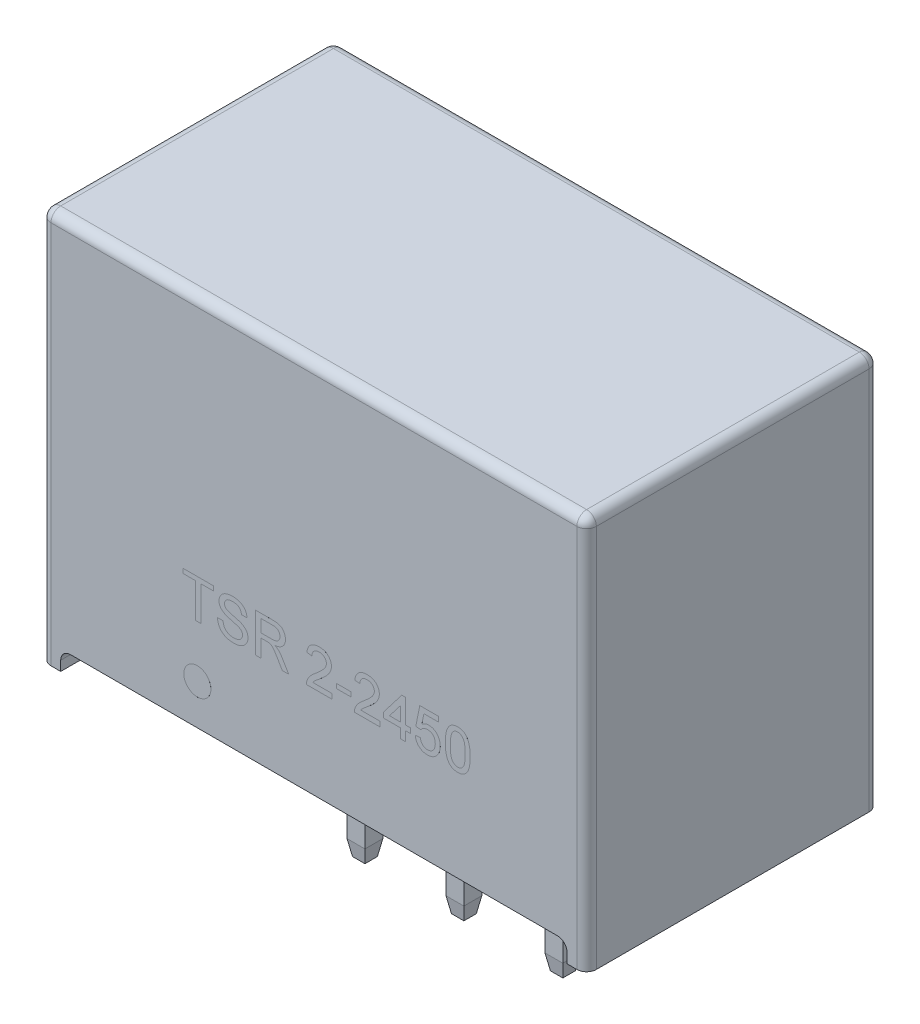
SolidWorks part; units mm, degrees
ref_plane "Front Plane" through (0, 0, 0) normal (0, 0, 1) x (1, 0, 0)
ref_plane "Top Plane" through (0, 0, 0) normal (0, 1, 0) x (1, 0, 0)
ref_plane "Right Plane" through (0, 0, 0) normal (1, 0, 0) x (0, 0, -1)
sketch "Sketch2" plane through (0, 0, 0) normal (0, 1, 0) x (1, 0, 0)
  line L1 (-7, -3.75) -> (7, -3.75)
  line L2 (-7, -3.75) -> (-7, 3.75)
  line L3 (-7, 3.75) -> (7, 3.75)
  line L4 (7, -3.75) -> (7, 3.75)
  line L5 (-7, -3.75) -> (7, 3.75) construction
  line L6 (-7, 3.75) -> (7, -3.75) construction
  point P0 (0, 0)
  dimension "D1" = 7.5
  dimension "D2" = 14
extrude "Boss-Extrude1" add sketch "Sketch2" along normal blind 10.1
sketch "Sketch3" plane through (0, 0, 0) normal (0, -1, 0) x (1, 0, 0)
  line L0 (-7, 3.75) -> (7, 3.75) construction
  line L1 (-6.5, -3.75) -> (6.5, -3.75)
  line L2 (-6.5, -3.75) -> (-6.5, 3.75)
  line L3 (-6.5, 3.75) -> (6.5, 3.75)
  line L4 (6.5, -3.75) -> (6.5, 3.75)
  line L5 (-6.5, -3.75) -> (6.5, 3.75) construction
  line L6 (-6.5, 3.75) -> (6.5, -3.75) construction
  point P0 (0, 0)
  dimension "D1" = 13
extrude "Cut-Extrude1" cut sketch "Sketch3" against normal blind 0.5
sketch "Sketch5" plane through (0, 0, 3.75) normal (0, 0, 1) x (1, 0, 0)
  circle A0 centre (-2.992, 1.5335) radius 0.348
  text T0 "TSR 2-2450" font "Century Gothic" height 1
  point P3 (-2.9059, 1.5335)
  point P4 (-2.992, 1.5335)
extrude "Boss-Extrude4" add sketch "Sketch5" along normal blind 0.0001
sketch "Sketch4" plane through (0, 0.5, 0) normal (0, -1, 0) x (1, 0, 0)
  line L0 (6.5, 3.75) -> (-6.5, 3.75) construction
  line L1 (2.27, 0.09) -> (2.73, 0.09)
  line L2 (2.27, 0.09) -> (2.27, -0.37)
  line L3 (2.27, -0.37) -> (2.73, -0.37)
  line L4 (2.73, 0.09) -> (2.73, -0.37)
  line L5 (2.27, 0.09) -> (2.73, -0.37) construction
  line L6 (2.27, -0.37) -> (2.73, 0.09) construction
  line L7 (7, 3.75) -> (7, -3.75) construction
  line L8 (-0.27, 0.09) -> (-0.27, -0.37)
  line L9 (-0.27, 0.09) -> (0.19, 0.09)
  line L10 (0.19, 0.09) -> (0.19, -0.37)
  line L11 (-0.27, -0.37) -> (0.19, -0.37)
  line L12 (-2.81, 0.09) -> (-2.81, -0.37)
  line L13 (-2.81, 0.09) -> (-2.35, 0.09)
  line L14 (-2.35, 0.09) -> (-2.35, -0.37)
  line L15 (-2.81, -0.37) -> (-2.35, -0.37)
  line L16 (2.27, 0.09) -> (-0.27, 0.09) construction
  point P0 (2.5, -0.14)
  dimension "D1" = 0.46
  dimension "D2" = 3.89
  dimension "D3" = 4.5
  dimension "D4" = 2.54
extrude "Boss-Extrude3" add sketch "Sketch4" along normal blind 4.6
fillet "Fillet1" radius 0.25 8 edges at (7, 5.05, 3.75) (7, 10.1, 0) (7, 5.05, -3.75) (-7, 5.05, -3.75) (0, 10.1, -3.75) (0, 10.1, 3.75) (-7, 10.1, 0) (-7, 5.05, 3.75)
fillet "Fillet2" radius 0.25 2 edges at (6.5, 0.5, 0) (-6.5, 0.5, 0)
chamfer "Chamfer2" distance 0.4 angle 10 12 edges at (2.5, -4.1, -0.37) (2.27, -4.1, -0.14) (2.5, -4.1, 0.09) (2.73, -4.1, -0.14) (-0.27, -4.1, -0.14) (-0.04, -4.1, 0.09) (0.19, -4.1, -0.14) (-0.04, -4.1, -0.37) (-2.81, -4.1, -0.14) (-2.58, -4.1, 0.09) (-2.35, -4.1, -0.14) (-2.58, -4.1, -0.37)
